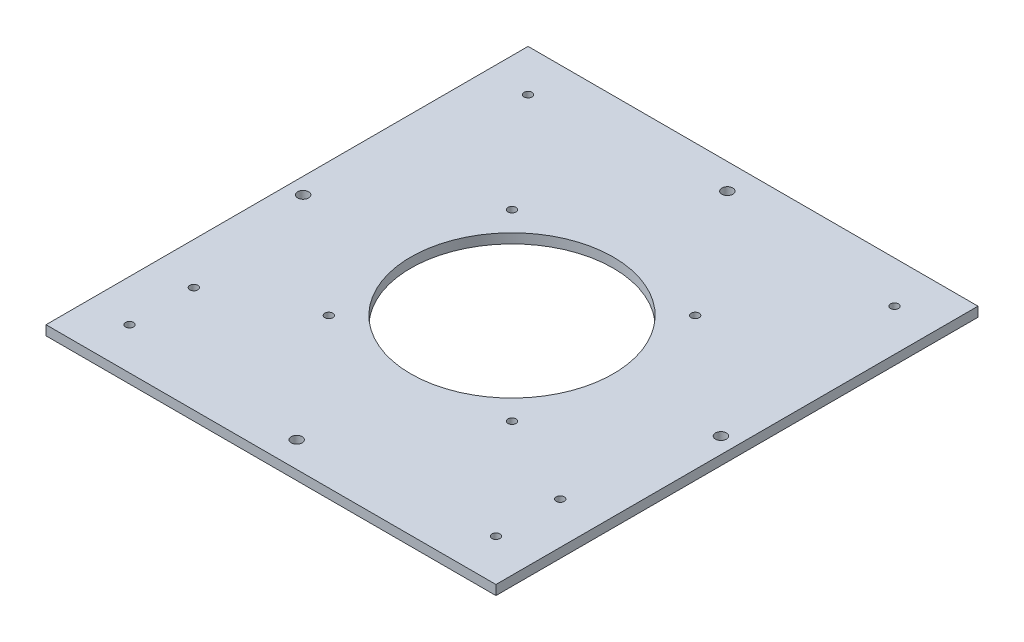
SolidWorks part; units mm, degrees
material "6061 合金"
ref_plane "前视基准面" through (0, 0, 0) normal (0, 0, 1) x (1, 0, 0)
ref_plane "上视基准面" through (0, 0, 0) normal (0, 1, 0) x (1, 0, 0)
ref_plane "右视基准面" through (0, 0, 0) normal (1, 0, 0) x (0, 0, -1)
sketch "草图1" plane through (0, 0, 0) normal (0, 0, 1) x (1, 0, 0)
  line L0 (12, 227.058) -> (152, 227.058)
  line L1 (12, 452.058) -> (12, 0) construction
  line L2 (152, 452.058) -> (152, 164.058) construction
  line L3 (152, 227.058) -> (12, 227.058) construction
extrude "拉伸-薄壁1" add sketch "草图1" along normal up to surface (150 mm away) thin contours L0
sketch "草图2" plane through (0, 224.058, 0) normal (0, -1, 0) x (1, 0, 0)
  circle A0 centre (82, 75) radius 31.5
  point P0 (82, 75)
  dimension "D1" = 63
extrude "切除-拉伸1" cut sketch "草图2" against normal up to next
sketch "草图3" plane through (0, 224.058, 0) normal (0, -1, 0) x (1, 0, 0)
  line L3 (82, 75) -> (82, 142) construction
  line L4 (53.5, 46.5) -> (110.5, 46.5) construction
  line L5 (53.5, 46.5) -> (53.5, 103.5) construction
  line L6 (53.5, 103.5) -> (110.5, 103.5) construction
  line L7 (110.5, 46.5) -> (110.5, 103.5) construction
  line L8 (53.5, 46.5) -> (110.5, 103.5) construction
  line L9 (53.5, 103.5) -> (110.5, 46.5) construction
  line L10 (152, 150) -> (12, 150) construction
  line L11 (82, 75) -> (147, 75) construction
  line L12 (82, 75) -> (82, 8) construction
  line L13 (82, 75) -> (17, 75) construction
  line L14 (152, 150) -> (152, 0) construction
  line L15 (25, 150) -> (25, 0) construction
  line L16 (139, 150) -> (139, 0) construction
  line L17 (25, 150) -> (25, 0)
  line L18 (139, 150) -> (139, 0)
  circle A0 centre (82, 75) radius 40.3051 construction
  circle A1 centre (82, 75) radius 44.5 construction
  point P17 (113.5104, 75)
  point P24 (139, 13)
  point P26 (25, 13)
  point P28 (25, 117)
  point P30 (25, 137)
  point P32 (139, 117)
  point P34 (139, 137)
  dimension "D3" = 89
  dimension "D1" = 57
  dimension "D2" = 57
  dimension "D4" = 8
  dimension "D5" = 5
hole_wizard "M3 螺纹孔的螺纹孔钻头1" positions "草图4" profile "草图5" hole size "M3" standard "GB" end condition through all
sketch "草图4" plane through (0, 224.058, 0) normal (0, -1, 0) x (-1, 0, 0)
  point P0 (-53.5, -103.5)
  point P3 (-53.5, -46.5)
  point P6 (-110.5, -46.5)
  point P9 (-110.5, -103.5)
sketch "草图5" plane through (53.5, 224.058, 103.5) normal (1, 0, 0) x (0, 0, -1)
  line L0 (0, 0) -> (0, 3)
  line L1 (0, 3) -> (1.25, 3)
  line L2 (1.25, 3) -> (1.25, 0)
  line L5 (1.25, 0) -> (0, 0)
  line L11 (0, -6.35) -> (0, 107.95) construction
  dimension "通孔孔直径" = 2.5
  dimension "通孔孔深度" = 3
hole_wizard "M3 间隙孔1" positions "草图6" profile "草图7" hole size "M3" standard "GB" end condition through all
sketch "草图6" plane through (0, 224.058, 0) normal (0, -1, 0) x (-1, 0, 0)
  point P0 (-82, -142)
  point P3 (-147, -75)
  point P6 (-82, -8)
  point P9 (-17, -75)
sketch "草图7" plane through (82, 224.058, 142) normal (1, 0, 0) x (0, 0, -1)
  line L0 (0, 0) -> (0, 3)
  line L1 (0, 3) -> (1.7, 3)
  line L2 (1.7, 3) -> (1.7, 0)
  line L5 (1.7, 0) -> (0, 0)
  line L11 (0, -6.35) -> (0, 107.95) construction
  dimension "通孔孔直径" = 3.4
  dimension "通孔孔深度" = 3
hole_wizard "M3 螺纹孔的螺纹孔钻头2" positions "草图8" profile "草图9" hole size "M3" standard "GB" end condition through all
sketch "草图8" plane through (0, 224.058, 0) normal (0, -1, 0) x (-1, 0, 0)
  point P0 (-139, -137)
  point P3 (-139, -117)
  point P6 (-139, -13)
  point P9 (-25, -137)
  point P12 (-25, -117)
  point P15 (-25, -13)
sketch "草图9" plane through (139, 224.058, 137) normal (1, 0, 0) x (0, 0, -1)
  line L0 (0, 0) -> (0, 3)
  line L1 (0, 3) -> (1.25, 3)
  line L2 (1.25, 3) -> (1.25, 0)
  line L5 (1.25, 0) -> (0, 0)
  line L11 (0, -6.35) -> (0, 107.95) construction
  dimension "通孔孔直径" = 2.5
  dimension "通孔孔深度" = 3
equation "\"D2@草图3\"=\"D1@草图3\""
